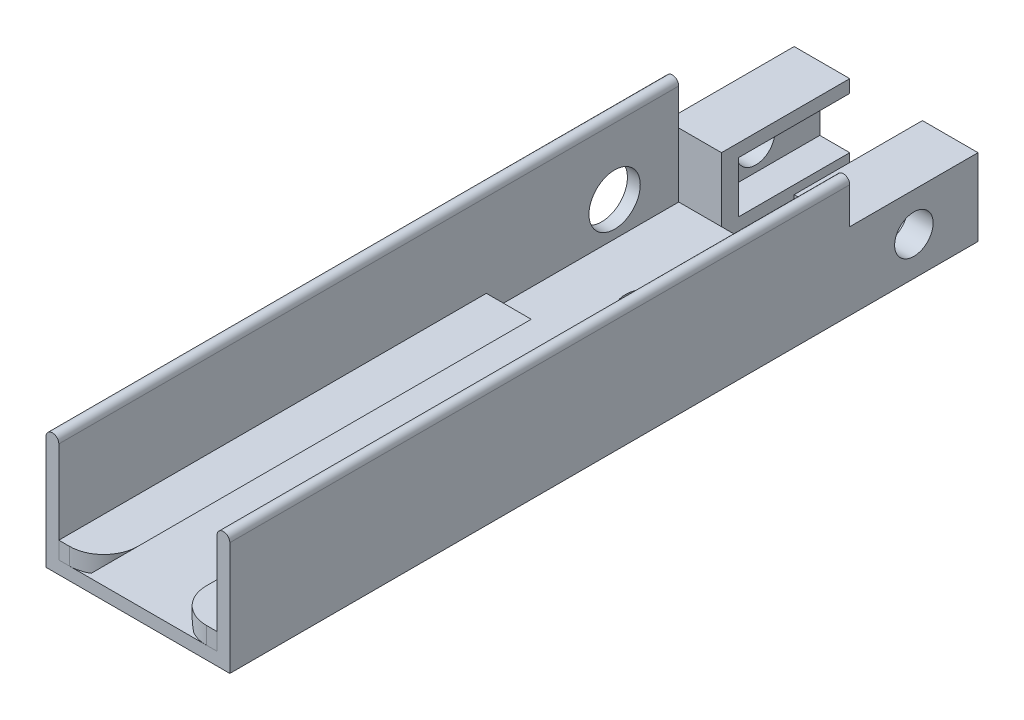
SolidWorks part; units mm, degrees
ref_plane "Front Plane" through (0, 0, 0) normal (0, 0, 1) x (1, 0, 0)
ref_plane "Top Plane" through (0, 0, 0) normal (0, 1, 0) x (1, 0, 0)
ref_plane "Right Plane" through (0, 0, 0) normal (1, 0, 0) x (0, 0, -1)
sketch "Sketch1" plane through (0, 0, 0) normal (0, 1, 0) x (1, 0, 0)
  line L1 (-2.15, 7.25) -> (2.15, 7.25)
  line L2 (-2.15, 7.25) -> (-2.15, -7.25)
  line L3 (-2.15, -7.25) -> (2.15, -7.25)
  line L4 (2.15, 7.25) -> (2.15, -7.25)
  line L5 (-2.15, 7.25) -> (2.15, -7.25) construction
  line L6 (-2.15, -7.25) -> (2.15, 7.25) construction
  point P0 (0, 0)
  dimension "D1" = 4.3
  dimension "D2" = 14.5
extrude "NP holder base" add sketch "Sketch1" along normal blind 2.5
shell "NP holder thickness" thickness 0.3
sketch "Sketch3" plane through (0, 0, 7.25) normal (0, 0, -1) x (-1, 0, 0)
  line L12 (-1.85, 0.3) -> (-1.85, 0.7)
  line L13 (-1.85, 2.5) -> (-1.85, 0.3) construction
  line L14 (-1.85, 0.7) -> (-0.8, 0.7)
  line L15 (-0.8, 0.7) -> (-1.2, 0.3)
  line L16 (-1.85, 0.3) -> (1.85, 0.3) construction
  line L17 (-1.2, 0.3) -> (-1.85, 0.3)
  line L18 (0, 1.375) -> (0, -1.375) construction
  line L19 (1.2, 0.3) -> (1.85, 0.3)
  line L20 (0.8, 0.7) -> (1.2, 0.3)
  line L21 (1.85, 0.7) -> (0.8, 0.7)
  line L22 (1.85, 0.3) -> (1.85, 0.7)
  dimension "D1" = 0.4
  dimension "D2" = 0.8
  dimension "D3" = 1.2
extrude "NP2.0 imec dovetail" add sketch "Sketch3" along normal blind 10
sketch "Sketch6" plane through (0, 0, 7.25) normal (0, 0, 1) x (1, 0, 0)
  line L6 (-2.15, 2.5) -> (-1.85, 2.5)
  line L7 (-2.15, 2.5) -> (-2.15, 2.65)
  line L8 (-1.85, 2.5) -> (-1.85, 2.65)
  line L9 (-2.15, 2.65) -> (-1.85, 2.65)
  line L10 (1.85, 2.5) -> (2.15, 2.5)
  line L11 (1.85, 2.5) -> (1.85, 2.65)
  line L12 (2.15, 2.5) -> (2.15, 2.65)
  line L13 (1.85, 2.65) -> (2.15, 2.65)
  arc A2 (-2.15, 2.65) -> (-1.85, 2.65) centre (-2, 2.65) cw
  arc A3 (1.85, 2.65) -> (2.15, 2.65) centre (2, 2.65) cw
  line M3 (-1.85, 2.5) -> (-2.15, 2.5)
  line M7 (2.15, 2.5) -> (1.85, 2.5)
  dimension "D1" = 0.15
  dimension "D2" = 0
extrude "inner piece rails" add sketch "Sketch6" against normal up to surface (14.5 mm away) contours L9 L7 L8 M3 | A2 L9 | A3 L13 | L13 L11 L12 M7 up to face at (0, 1.325, -7.25)
sketch "Sketch7" plane through (0, 0, -7.25) normal (0, 0, -1) x (-1, 0, 0)
  line L1 (-2.15, 0) -> (-1.55, 0)
  line L2 (-2.15, 0) -> (-2.15, 1.8)
  line L3 (-2.15, 1.8) -> (-1.55, 1.8)
  line L4 (-1.55, 0) -> (-1.55, 1.8)
  line L5 (-1.55, 1.8) -> (-0.85, 1.8)
  line L10 (0, 1.54) -> (0, -1.54) construction
  line L12 (-1.55, 1.8) -> (-1.55, 1.4)
  line L15 (-1.55, 0) -> (-0.85, 0)
  line L16 (-1.55, 0) -> (-1.55, 0.3)
  line L17 (-1.55, 0.3) -> (-0.85, 0.3)
  line L18 (-0.85, 0) -> (-0.85, 0.3)
  line L19 (0.85, 0) -> (0.85, 0.3)
  line L20 (1.55, 0.3) -> (0.85, 0.3)
  line L21 (1.55, 0) -> (1.55, 0.3)
  line L22 (1.55, 0) -> (0.85, 0)
  line L27 (1.55, 0) -> (1.55, 1.8)
  line L28 (2.15, 1.8) -> (1.55, 1.8)
  line L29 (2.15, 0) -> (2.15, 1.8)
  line L30 (2.15, 0) -> (1.55, 0)
  line L31 (-1.55, 1.8) -> (-1.55, 1.5)
  line L32 (-1.55, 1.5) -> (-0.85, 1.5)
  line L33 (-0.85, 1.8) -> (-0.85, 1.5)
  line L34 (1.55, 1.8) -> (0.85, 1.8)
  line L35 (1.55, 1.8) -> (1.55, 1.5)
  line L36 (1.55, 1.5) -> (0.85, 1.5)
  line L37 (0.85, 1.8) -> (0.85, 1.5)
  dimension "D1" = 1.8
  dimension "D2" = 0
  dimension "D3" = 0.6
  dimension "D4" = 0.7
  dimension "D5" = 0.3
  dimension "D6" = 0.3
  dimension "D7" = 0
  dimension "D8" = 0
extrude "extraction hooks" add sketch "Sketch7" along normal blind 3
sketch "Sketch8" plane through (2.15, 0, 0) normal (1, 0, 0) x (0, 0, -1)
  line L9 (10.25, 1.8) -> (10.25, 0) construction
  circle A1 centre (8.75, 0.9) radius 0.45
  point P4 (10.25, 0.9)
  dimension "D1" = 0
  dimension "D3" = 0.9
  dimension "D2" = 1.5
extrude "extraction hole" cut sketch "Sketch8" against normal up to surface (4.3 mm away) up to face at (-2.15, 1.4833, -3.4167)
sketch "Sketch15" plane through (0, 0, -7.25) normal (0, 0, 1) x (1, 0, 0)
  line L0 (1.85, 0.3) -> (1.2, 0.3) construction
  line L21 (1.55, 1.5) -> (0.85, 1.5)
  line L34 (-0.85, 1.5) -> (-1.55, 1.5)
  line L35 (-0.85, 1.5) -> (-0.85, 0.3)
  line L36 (-0.85, 0.3) -> (-1.55, 0.3)
  line L37 (-1.55, 1.5) -> (-1.55, 0.3)
  line L38 (1.55, 1.5) -> (1.55, 0.3)
  line L39 (1.55, 0.3) -> (0.85, 0.3)
  line L40 (0.85, 1.5) -> (0.85, 0.3)
  dimension "D1" = 0
extrude "extractionstopper" add sketch "Sketch15" against normal blind 0.4
sketch "Sketch12" plane through (0, 0, 0) normal (0, -1, 0) x (1, 0, 0)
  line L0 (0.85, -7.25) -> (-0.85, -7.25) construction
  circle A0 centre (0, -4.75) radius 0.6
  dimension "D3" = 1.2
  dimension "D1" = 0
  dimension "D2" = 2.5
extrude "adhesive Hole" cut sketch "Sketch12" against normal up to surface (0.3 mm away) up to face at (-1.2, 0.3, -8.95)
sketch "Sketch13" plane through (-2.15, 0, 0) normal (-1, 0, 0) x (0, 0, 1)
  line L0 (-7.25, 2.65) -> (-7.25, 1.8) construction
  line L1 (-10.25, 0) -> (7.25, 0) construction
  circle A0 centre (-5.75, 1.1) radius 0.6
  dimension "D1" = 1.2
  dimension "D2" = 1.5
  dimension "D3" = 1.1
extrude "vertical anchor hole" cut sketch "Sketch13" against normal up to surface (0.3 mm away)
sketch "Sketch16" plane through (0, 0.7, 0) normal (0, 1, 0) x (1, 0, 0)
  line L0 (-1.6, -7.25) -> (-0.8, -7.25)
  line L1 (-1.85, -7.25) -> (-0.8, -7.25) construction
  line L2 (-0.8, -7.25) -> (-0.8, -6.45)
  line L3 (-0.8, 2.75) -> (-0.8, -7.25) construction
  line L4 (0, -1.54) -> (0, 1.54) construction
  line L5 (0.8, -7.25) -> (0.8, -6.45)
  line L6 (1.6, -7.25) -> (0.8, -7.25)
  arc A0 (-1.6, -7.25) -> (-0.8, -6.45) centre (-1.6, -6.45) ccw
  arc A1 (1.6, -7.25) -> (0.8, -6.45) centre (1.6, -6.45) cw
  dimension "D1" = 0.8
  dimension "D2" = 0.8
extrude "entry edge smoothing" cut sketch "Sketch16" against normal up to surface (0.4 mm away) up to face at (-1.2, 0.3, -8.95)
